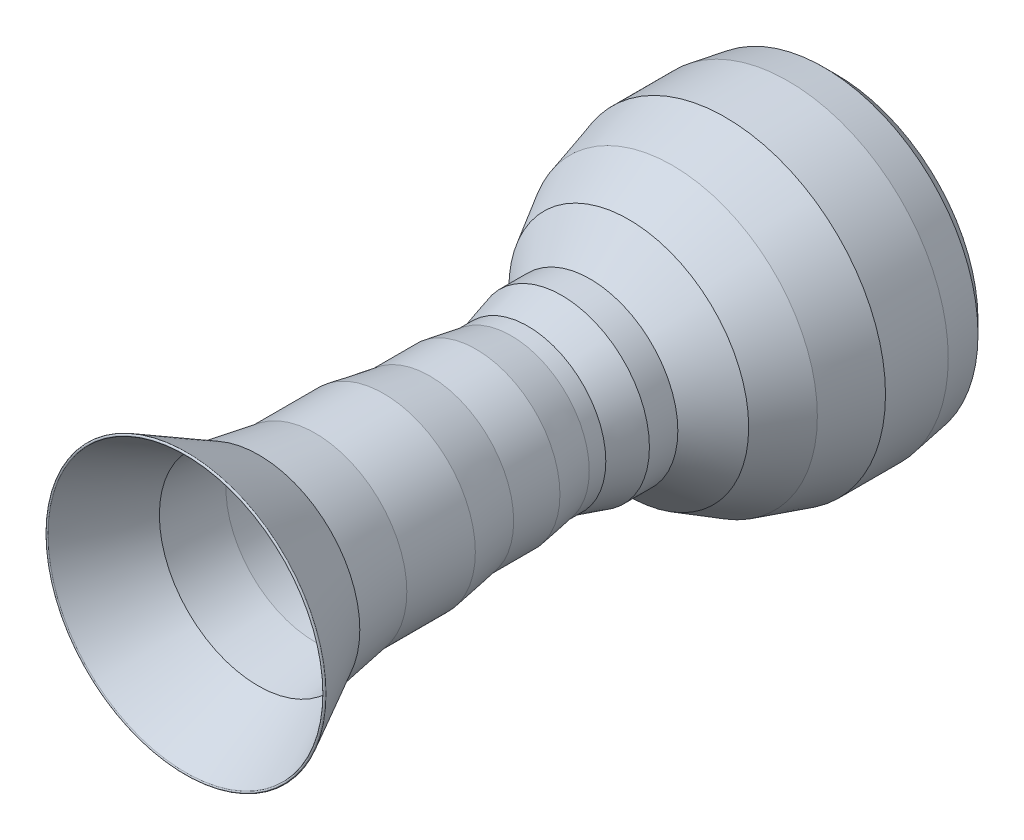
SolidWorks part; units mm, degrees
ref_plane "Front Plane" through (0, 0, 0) normal (0, 0, 1) x (1, 0, 0)
ref_plane "Top Plane" through (0, 0, 0) normal (0, 1, 0) x (1, 0, 0)
ref_plane "Right Plane" through (0, 0, 0) normal (1, 0, 0) x (0, 0, -1)
sketch "Sketch1" plane through (0, 0, 0) normal (1, 0, 0) x (0, 0, -1)
  line L0 (31.8024, 848.4909) -> (1294.8478, 848.4909) construction
  line L1 (0, 0) -> (4289.3111, 0) construction
sketch "Sketch4" plane through (0, 0, 0) normal (1, 0, 0) x (0, 0, -1)
  line L0 (1240.3005, 594.5388) -> (1554.3952, 427.2173)
  line L1 (1554.3952, 427.2173) -> (1800.9743, 386.1208)
  line L2 (1800.9743, 386.1208) -> (2097.4562, 386.1208)
  line L3 (2097.4562, 386.1208) -> (2296.4331, 352.958)
  line L4 (2296.4331, 352.958) -> (2496.6794, 352.958)
  line L5 (2496.6794, 352.958) -> (2648.8647, 327.5938)
  line L6 (2648.8647, 327.5938) -> (2722.7102, 327.5938)
  line L7 (2722.7102, 327.5938) -> (2869.4834, 369.5394)
  line L8 (2869.4834, 369.5394) -> (2981.0311, 369.5394)
  line L9 (2981.0311, 369.5394) -> (2981.0311, 327.5938)
  line L10 (2981.0311, 327.5938) -> (3164.3153, 510.8781)
  line L11 (3164.3153, 510.8781) -> (3350.8996, 618.0225)
  line L12 (3350.8996, 618.0225) -> (3577.7017, 682.8392)
  line L13 (3577.7017, 682.8392) -> (3846.9931, 682.8392)
  line L14 (3846.9931, 682.8392) -> (3997.4542, 657.7624)
  line L15 (3997.4542, 657.7624) -> (4049.2381, 605.9785)
  line L16 (1245.0021, 603.3646) -> (1557.6529, 436.8123)
  line L17 (1557.6529, 436.8123) -> (1801.8019, 396.1208)
  line L18 (1801.8019, 396.1208) -> (2098.2838, 396.1208)
  line L19 (2098.2838, 396.1208) -> (2297.2607, 362.958)
  line L20 (2297.2607, 362.958) -> (2497.507, 362.958)
  line L21 (2497.507, 362.958) -> (2649.6923, 337.5938)
  line L22 (2649.6923, 337.5938) -> (2721.3093, 337.5938)
  line L23 (2721.3093, 337.5938) -> (2868.0825, 379.5394)
  line L24 (2868.0825, 379.5394) -> (2991.0311, 379.5394)
  line L25 (2991.0311, 379.5394) -> (2991.0311, 351.7359)
  line L26 (2991.0311, 351.7359) -> (3158.1836, 518.8885)
  line L27 (3158.1836, 518.8885) -> (3346.9782, 627.3022)
  line L28 (3346.9782, 627.3022) -> (3576.3008, 692.8392)
  line L29 (3576.3008, 692.8392) -> (3847.8208, 692.8392)
  line L30 (3847.8208, 692.8392) -> (4002.2592, 667.0995)
  line L31 (4002.2592, 667.0995) -> (4056.3091, 613.0496)
  arc A0 (1240.3005, 594.5388) -> (1245.0021, 603.3646) centre (1242.6513, 598.9517) cw
  arc A1 (4049.2381, 605.9785) -> (4056.3091, 613.0496) centre (4052.7736, 609.5141) ccw
revolve "Revolve4" add sketch "Sketch4" angle 360 about L1
